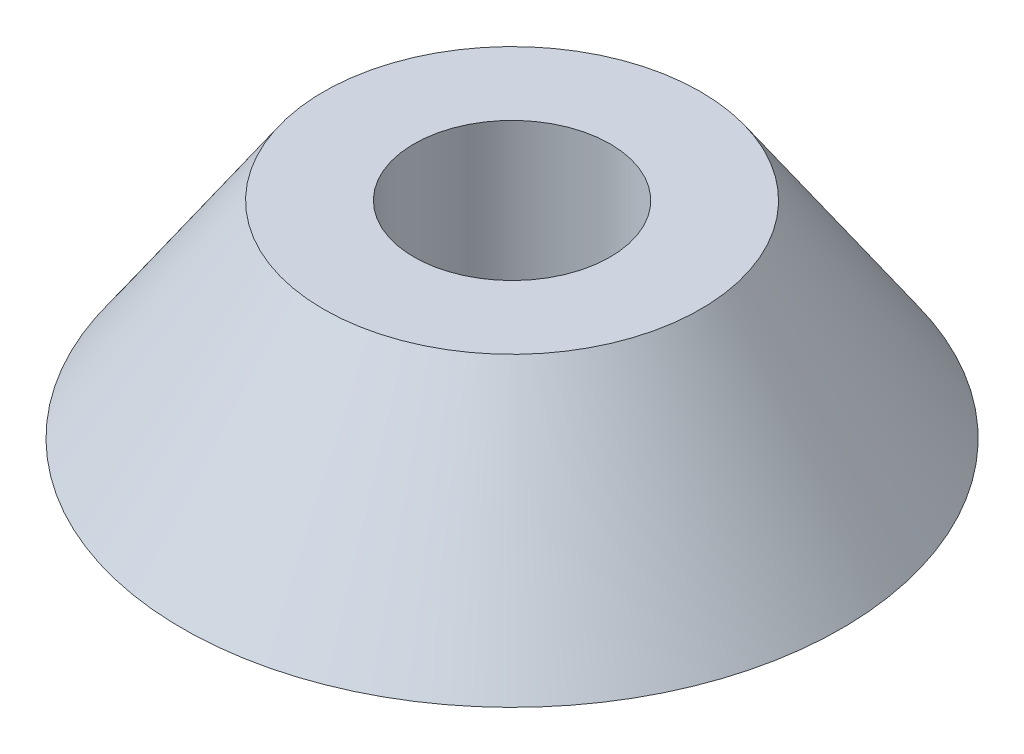
SolidWorks part; units mm, degrees
material "6061-T6 (SS)"
ref_plane "Front Plane" through (0, 0, 0) normal (0, 0, 1) x (1, 0, 0)
ref_plane "Top Plane" through (0, 0, 0) normal (0, 1, 0) x (1, 0, 0)
ref_plane "Right Plane" through (0, 0, 0) normal (1, 0, 0) x (0, 0, -1)
sketch "Sketch1" plane through (0, 0, 0) normal (0, 0, 1) x (1, 0, 0)
  line L0 (4.7625, 0) -> (4.7625, 10)
  line L1 (4.7625, 10) -> (9.15, 10)
  line L2 (9.15, 10) -> (16, 0)
  line L3 (16, 0) -> (4.7625, 0)
  line L4 (0, 0) -> (0, 15.0979) construction
  dimension "D1" = 10
  dimension "D2" = 9.525
  dimension "D3" = 18.3
  dimension "D4" = 32
revolve "Revolve1" add sketch "Sketch1" angle 360 about L4
